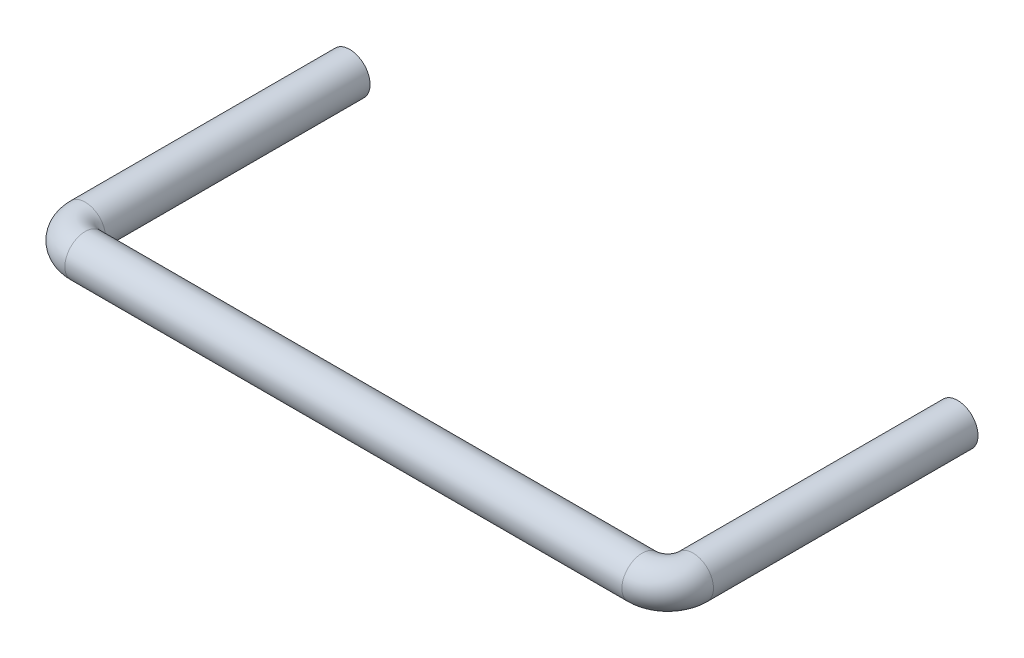
SolidWorks part; units mm, degrees
ref_plane "Front" through (0, 0, 0) normal (0, 0, 1) x (1, 0, 0)
ref_plane "Top" through (0, 0, 0) normal (0, 1, 0) x (1, 0, 0)
ref_plane "Right" through (0, 0, 0) normal (1, 0, 0) x (0, 0, -1)
sketch "Sketch1" plane through (0, 0, 0) normal (0, 1, 0) x (1, 0, 0)
  line L0 (0, 0) -> (0, -11.4) construction
  line L1 (-10.95, -11.4) -> (10.95, -11.4)
  line L2 (11.95, -10.4) -> (11.95, 0)
  line L3 (-11.95, -10.4) -> (-11.95, 0)
  arc A0 (10.95, -11.4) -> (11.95, -10.4) centre (10.95, -10.4) ccw
  arc A1 (-11.95, -10.4) -> (-10.95, -11.4) centre (-10.95, -10.4) ccw
  point P11 (11.95, -11.4)
  point P14 (-11.95, -11.4)
  dimension "D3" = 1
  dimension "D1" = 11.4
  dimension "D2" = 23.9
sweep "Sweep1" add path "Sketch1" circular profile diameter 1.6 parameters "D3"=1.6
ref_plane "Plane1" through (-11.95, 0, 0) normal (1, 0, 0) x (0, 0, -1)
ref_plane "Plane2" through (11.95, 0, 0) normal (1, 0, 0) x (0, 0, -1)
